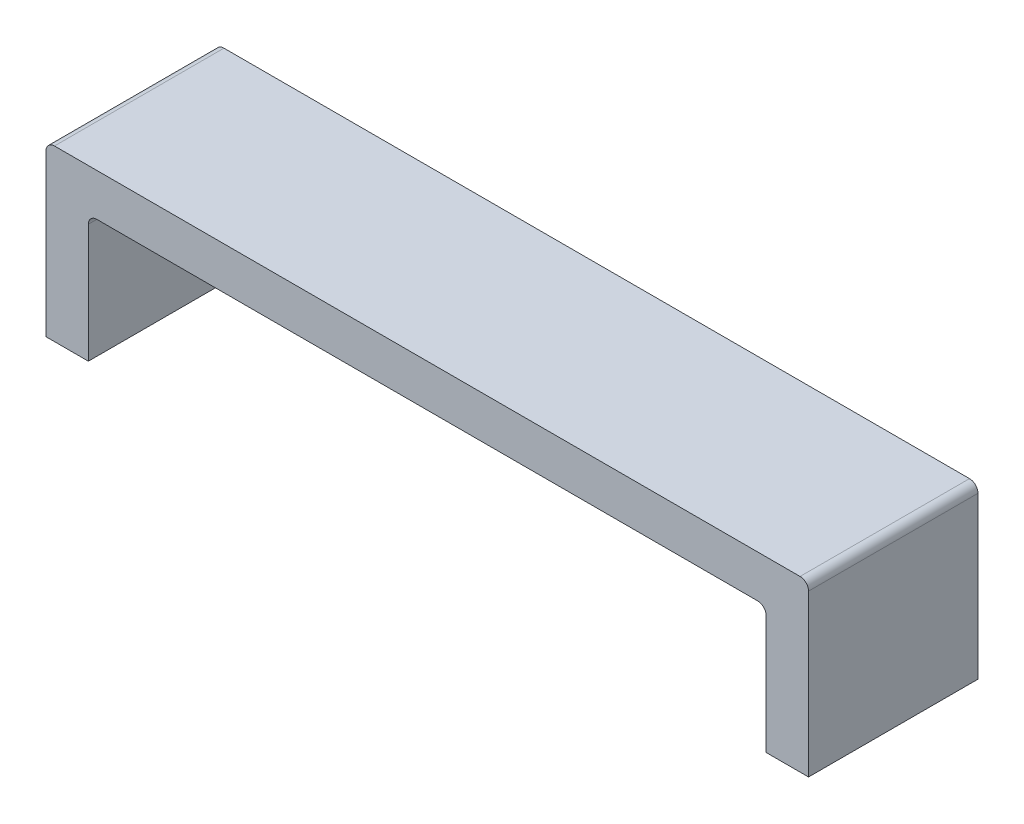
SolidWorks part; units mm, degrees
ref_plane "Front Plane" through (0, 0, 0) normal (0, 0, 1) x (1, 0, 0)
ref_plane "Top Plane" through (0, 0, 0) normal (0, 1, 0) x (1, 0, 0)
ref_plane "Right Plane" through (0, 0, 0) normal (1, 0, 0) x (0, 0, -1)
sketch "Sketch1" plane through (0, 0, 0) normal (0, 0, 1) x (1, 0, 0)
  line L0 (0, 0) -> (0, 101.6)
  line L6 (25.4, 76.2) -> (25.4, 0)
  line L7 (25.4, 0) -> (0, 0)
  line L8 (0, 101.6) -> (457.2, 101.6)
  line L10 (431.8, 76.2) -> (25.4, 76.2)
  line L11 (457.2, 0) -> (457.2, 101.6)
  line L12 (431.8, 76.2) -> (431.8, 0)
  line L13 (431.8, 0) -> (457.2, 0)
  dimension "D1" = 101.6
  dimension "D2" = 25.4
  dimension "D3" = 25.4
  dimension "D4" = 457.2
  dimension "D5" = 25.4
extrude "Boss-Extrude1" add sketch "Sketch1" along normal blind 101.6
fillet "Fillet1" radius 5.08 4 edges at (431.8, 76.2, 50.8) (25.4, 76.2, 50.8) (457.2, 101.6, 50.8) (0, 101.6, 50.8)
